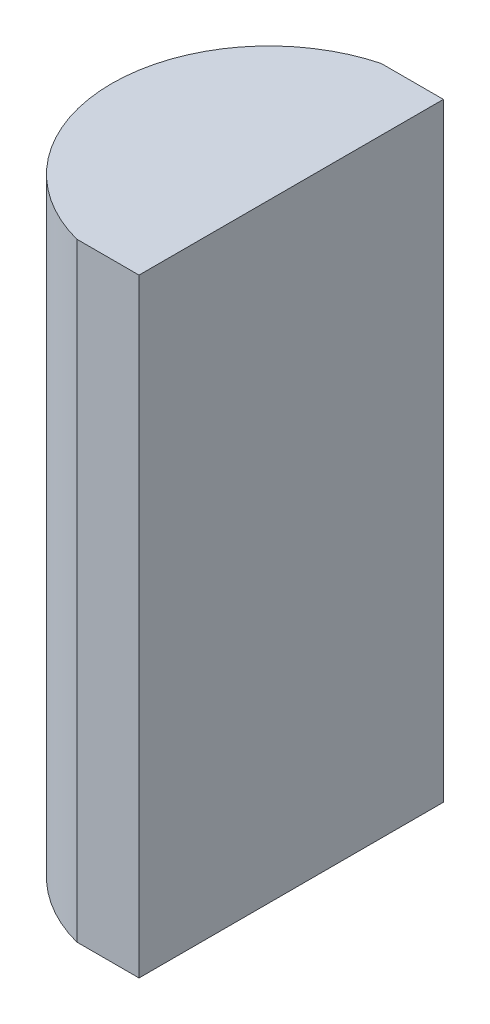
SolidWorks part; units mm, degrees
ref_plane "前视基准面" through (0, 0, 0) normal (0, 0, 1) x (1, 0, 0)
ref_plane "上视基准面" through (0, 0, 0) normal (0, 1, 0) x (1, 0, 0)
ref_plane "右视基准面" through (0, 0, 0) normal (1, 0, 0) x (0, 0, -1)
sketch "草图1" plane through (0, 0, 0) normal (0, 1, 0) x (1, 0, 0)
  line L0 (10.7432, 0) -> (-19.1624, 0) construction
  line L1 (3.0403, 5) -> (5.0852, 5)
  line L2 (3.0403, -5) -> (5.0852, -5)
  line L3 (5.0852, 5) -> (5.0852, -5)
  arc A0 (3.0403, 5) -> (3.0403, -5) centre (4.3552, 0) ccw
  point P19 (-0.8148, 0)
  point P20 (5.0852, 0)
  dimension "D2" = 5
  dimension "D3" = 5.17
  dimension "D4" = 5.9
  dimension "D1" = 5
extrude "凸台-拉伸1" add sketch "草图1" along normal blind 20
